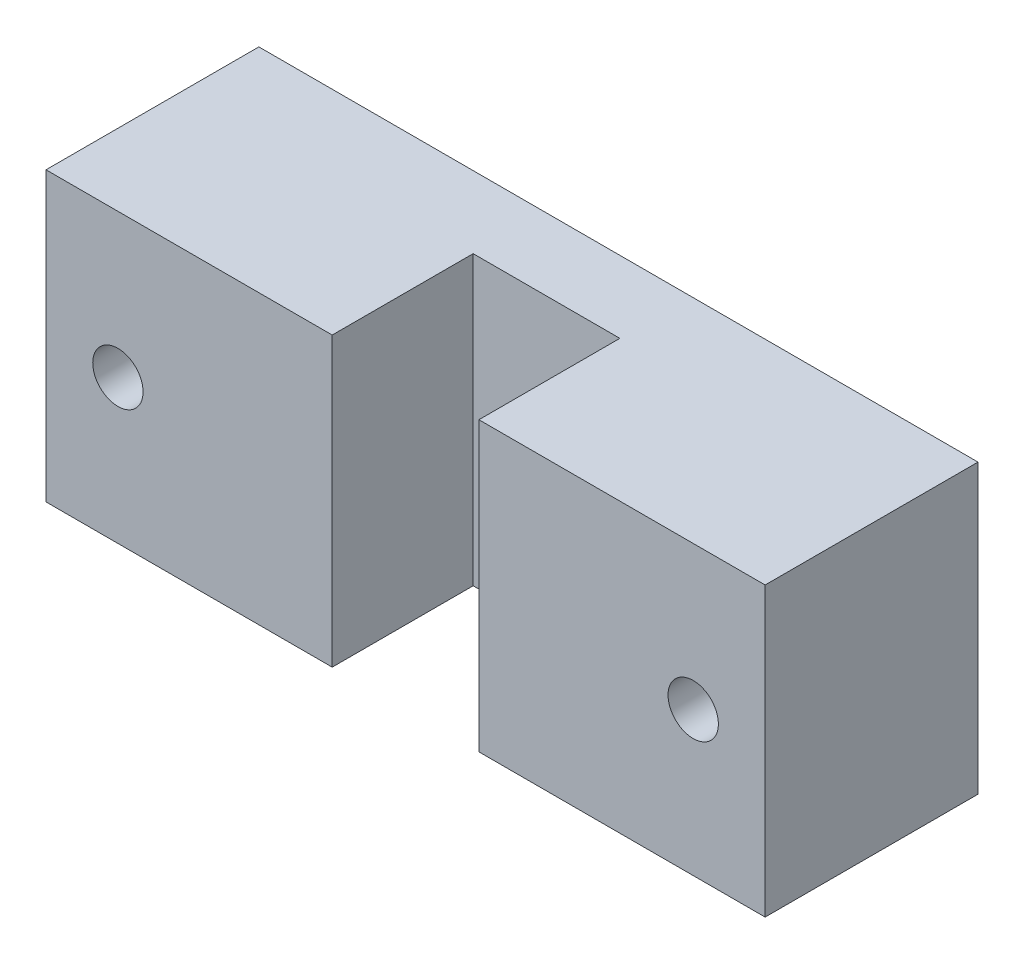
SolidWorks part; units mm, degrees
ref_plane "Спереди" through (0, 0, 0) normal (0, 0, 1) x (1, 0, 0)
ref_plane "Сверху" through (0, 0, 0) normal (0, 1, 0) x (1, 0, 0)
ref_plane "Справа" through (0, 0, 0) normal (1, 0, 0) x (0, 0, -1)
sketch "Sketch2" plane through (0, 0, 0) normal (0, 0, 1) x (1, 0, 0)
  line L0 (20, 0) -> (-20, 0) construction
  line L1 (25, -10) -> (-25, -10)
  line L2 (25, -10) -> (25, 10)
  line L3 (25, 10) -> (-25, 10)
  line L4 (-25, -10) -> (-25, 10)
  line L5 (25, -10) -> (-25, 10) construction
  line L6 (25, 10) -> (-25, -10) construction
  circle A0 centre (-20, 0) radius 1.75
  circle A1 centre (20, 0) radius 1.75
  point P0 (0, 0)
  point P9 (0, 0)
  dimension "D4" = 3.5
  dimension "D1" = 20
  dimension "D2" = 50
  dimension "D3" = 40
extrude "Boss-Extrude1" add sketch "Sketch2" along normal blind 5
sketch "Sketch5" plane through (0, -10, 0) normal (0, -1, 0) x (1, 0, 0)
  line L0 (-25, 5) -> (-25, 14.8)
  line L1 (-25, 5) -> (25, 5) construction
  line L2 (-25, 14.8) -> (-5.1, 14.8)
  line L3 (-5.1, 14.8) -> (-5.1, 5)
  line L4 (-5.1, 5) -> (5.1, 5)
  line L5 (5.1, 5) -> (5.1, 14.8)
  line L6 (5.1, 14.8) -> (25, 14.8)
  line L7 (25, 14.8) -> (25, 5)
  line L8 (25, 5) -> (-25, 5) construction
  line L9 (-25, 0) -> (25, 0) construction
  line L10 (0, 5) -> (0, 0) construction
  line L11 (25, 5) -> (25, 0) construction
  arc A0 (-25, 5) -> (25, 5) centre (0, 65) ccw
  point P15 (0, 0)
  dimension "D1" = 10.2
  dimension "D3" = 9.8
extrude "Boss-Extrude2" add sketch "Sketch5" against normal up to surface (20 mm away) up to face at (0, 10, 2.5)
sketch "Sketch6" plane through (0, 0, 0) normal (0, 0, -1) x (-1, 0, 0)
  circle A0 centre (20, 0) radius 1.75
  circle A1 centre (-20, 0) radius 1.75
  circle A2 centre (-20, 0) radius 1.75 construction
extrude "Cut-Extrude1" cut sketch "Sketch6" against normal through all
